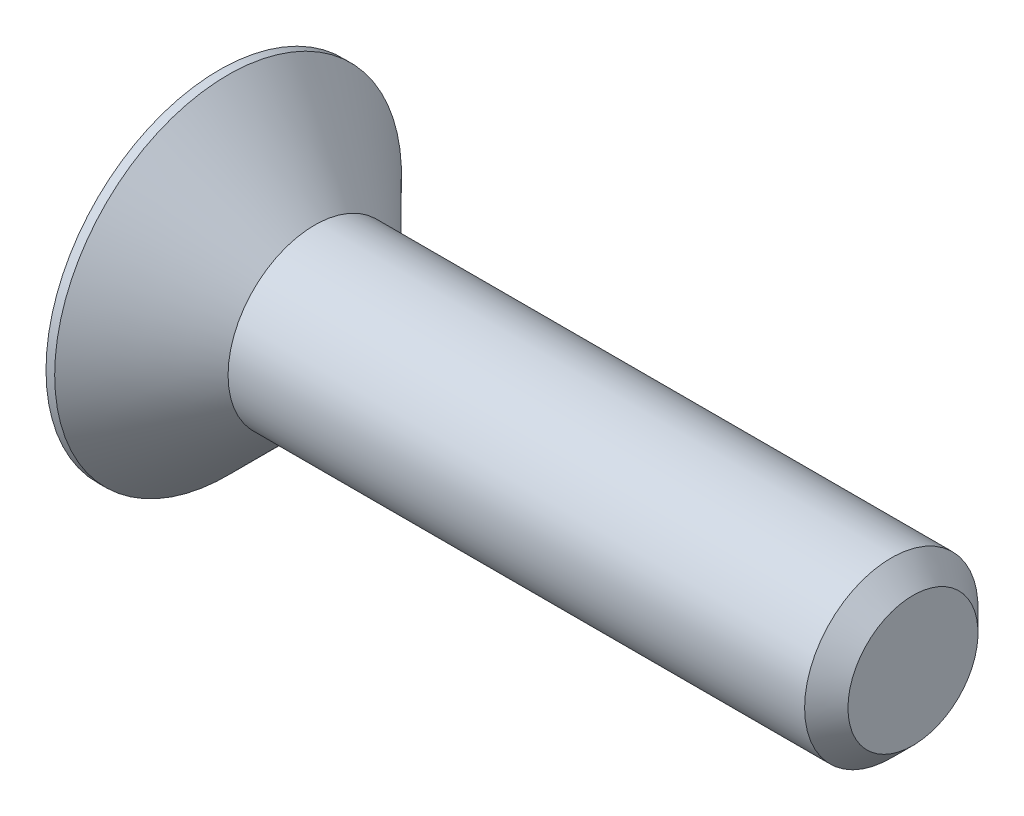
SolidWorks part; units mm, degrees
ref_plane "Front Plane" through (0, 0, 0) normal (0, 0, 1) x (1, 0, 0)
ref_plane "Top Plane" through (0, 0, 0) normal (0, 1, 0) x (1, 0, 0)
ref_plane "Right Plane" through (0, 0, 0) normal (1, 0, 0) x (0, 0, -1)
sketch "Sketch2" plane through (0, 0, 0) normal (0, 0, 1) x (1, 0, 0)
  line L0 (0, 0) -> (0, 2)
  line L1 (0, 2) -> (0.1, 2)
  line L2 (0.1, 2) -> (1.1, 1)
  line L3 (1.1, 1) -> (7.75, 1)
  line L4 (7.75, 1) -> (8, 0.75)
  line L5 (8, 0.75) -> (8, 0)
  line L6 (8, 0) -> (0, 0)
  line L7 (-2.2818, 0) -> (8.0811, 0) construction
  dimension "D1" = 4
  dimension "D2" = 0.1
  dimension "D3" = 45
  dimension "D4" = 8
  dimension "D5" = 0.25
  dimension "D6" = 2
revolve "Revolve1" add sketch "Sketch2" angle 360 about L7
sketch "Sketch3" plane through (0, 0, 0) normal (-1, 0, 0) x (0, 0, 1)
  line L1 (0.433, -0.75) -> (0.866, 0)
  line L2 (0.866, 0) -> (0.433, 0.75)
  line L3 (0.433, 0.75) -> (-0.433, 0.75)
  line L4 (-0.433, 0.75) -> (-0.866, 0)
  line L5 (-0.866, 0) -> (-0.433, -0.75)
  line L6 (-0.433, -0.75) -> (0.433, -0.75)
  circle A0 centre (0, 0) radius 0.75 construction
  dimension "D1" = 1.5
extrude "Cut-Extrude1" cut sketch "Sketch3" against normal blind 0.8
